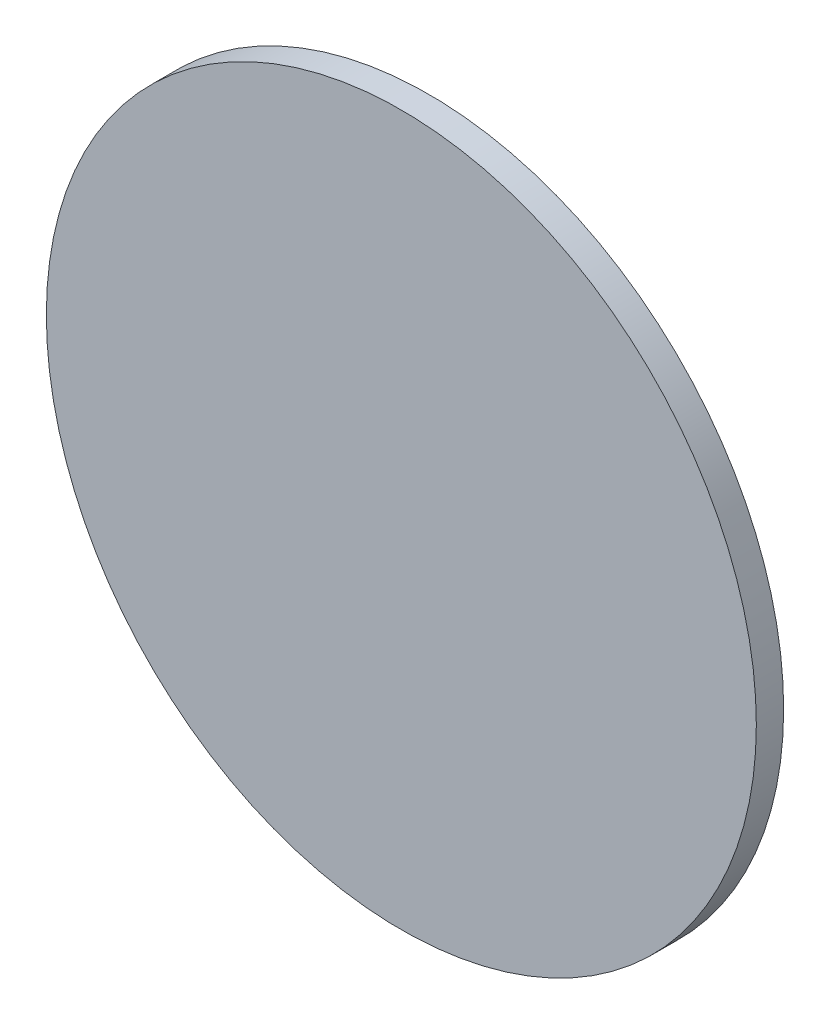
SolidWorks part; units mm, degrees
ref_plane "Front Plane" through (0, 0, 0) normal (0, 0, 1) x (1, 0, 0)
ref_plane "Top Plane" through (0, 0, 0) normal (0, 1, 0) x (1, 0, 0)
ref_plane "Right Plane" through (0, 0, 0) normal (1, 0, 0) x (0, 0, -1)
sketch "Sketch1" plane through (0, 0, 0) normal (0, 0, 1) x (1, 0, 0)
  circle A2 centre (-31.5327, 19.9145) radius 165.0623
extrude "Boss-Extrude1" add sketch "Sketch1" along normal blind 12.7
